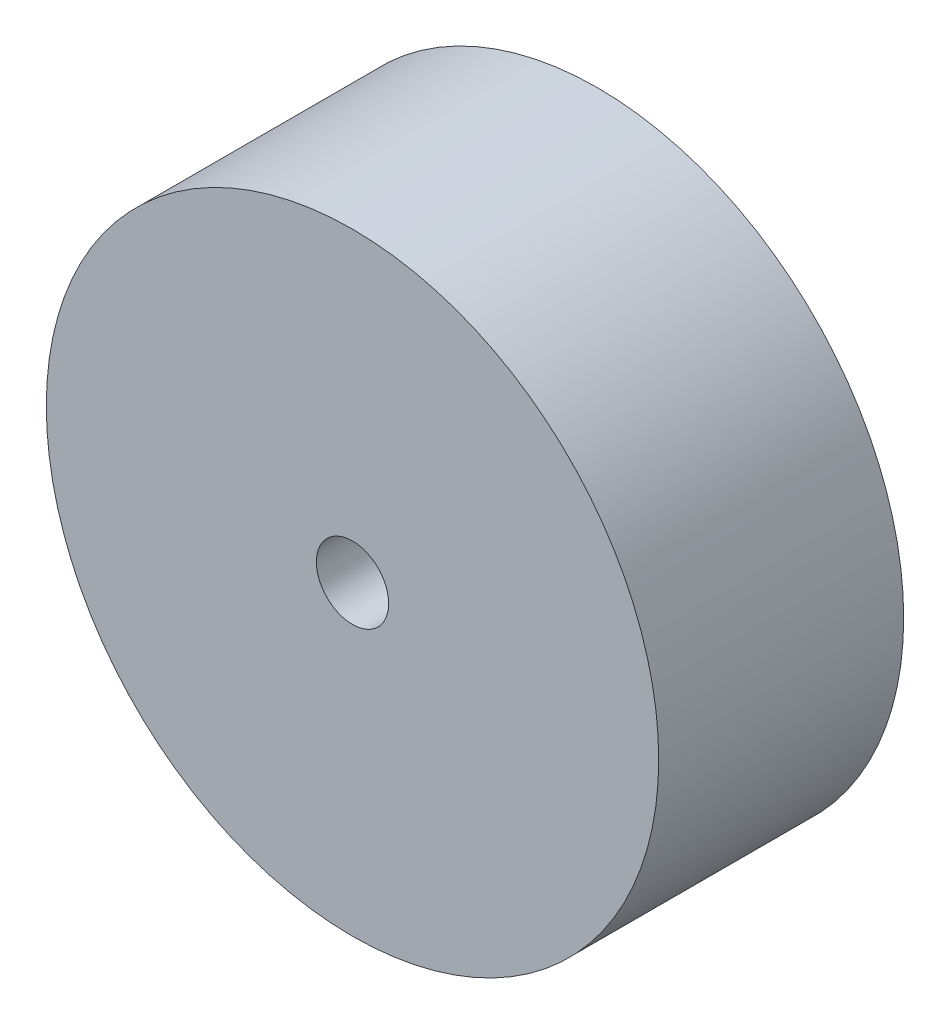
SolidWorks part; units mm, degrees
ref_plane "Front Plane" through (0, 0, 0) normal (0, 0, 1) x (1, 0, 0)
ref_plane "Top Plane" through (0, 0, 0) normal (0, 1, 0) x (1, 0, 0)
ref_plane "Right Plane" through (0, 0, 0) normal (1, 0, 0) x (0, 0, -1)
sketch "Sketch1" plane through (0, 0, 0) normal (0, 0, 1) x (1, 0, 0)
  circle A0 centre (0, 0) radius 25.4
  circle A1 centre (0, 0) radius 3
  dimension "D1" = 50.8
  dimension "D2" = 6
extrude "Boss-Extrude1" add sketch "Sketch1" along normal blind 20.32
